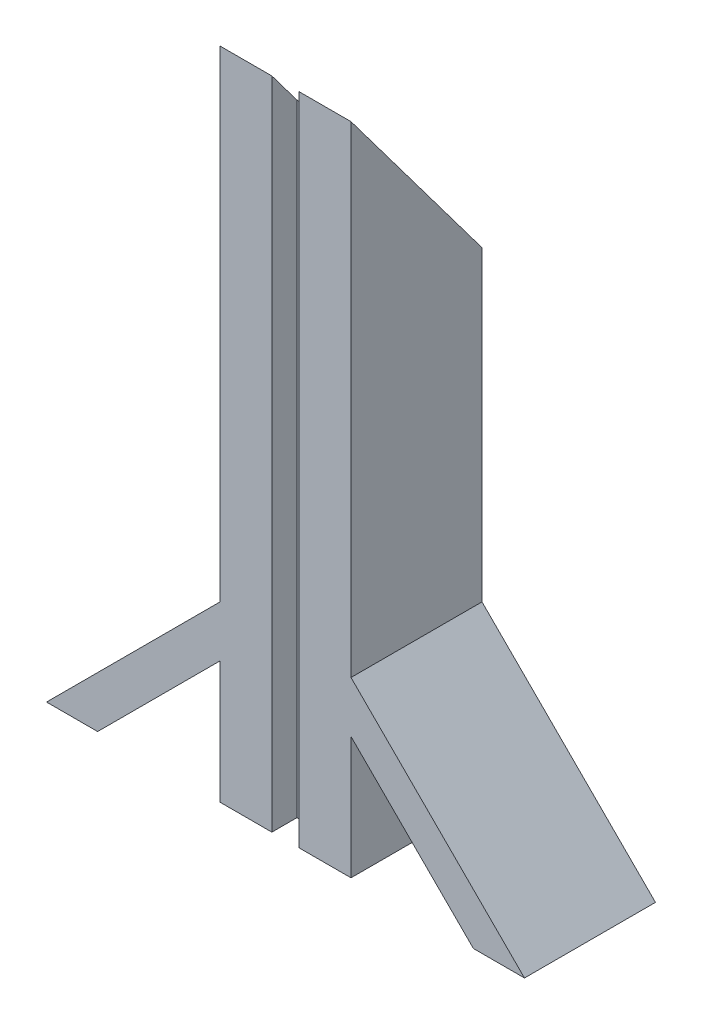
SolidWorks part; units mm, degrees
ref_plane "Front Plane" through (0, 0, 0) normal (0, 0, 1) x (1, 0, 0)
ref_plane "Top Plane" through (0, 0, 0) normal (0, 1, 0) x (1, 0, 0)
ref_plane "Right Plane" through (0, 0, 0) normal (1, 0, 0) x (0, 0, -1)
sketch "Sketch1" plane through (0, 0, 0) normal (0, 1, 0) x (1, 0, 0)
  line L1 (-15, -15) -> (15, -15)
  line L2 (-15, -15) -> (-15, 15)
  line L3 (-15, 15) -> (15, 15)
  line L4 (15, -15) -> (15, 15)
  line L5 (0, 15) -> (0, -15) construction
  line L6 (-15, 0) -> (15, 0) construction
  point P0 (0, 0)
  dimension "D1" = 30
extrude "Boss-Extrude1" add sketch "Sketch1" along normal blind 150
sketch "Sketch2" plane through (0, 0, 0) normal (0, 0, 1) x (1, 0, 0)
  line L0 (15, 39.7364) -> (54.7364, 0)
  line L1 (15, 150) -> (15, 0) construction
  line L4 (54.7364, 0) -> (43.0338, 0)
  line L5 (43.0338, 0) -> (15, 28.0338)
  line L6 (15, 39.7364) -> (15, 28.0338)
  dimension "D1" = 45
extrude "Boss-Extrude2" add sketch "Sketch2" along normal up to surface (15 mm away) and the other way up to surface (15 mm away) up to face at (0, 75, 15) other way up to face at (0, 75, -15)
mirror "Mirror1" about plane through (0, 0, 0) normal (1, 0, 0) of "Boss-Extrude2"
sketch "Sketch3" plane through (-15, 0, 0) normal (-1, 0, 0) x (0, 0, 1)
  line L0 (15, 150) -> (-15, 110)
  line L1 (-15, 150) -> (-15, 39.7364) construction
  line L2 (-15, 110) -> (-15, 150)
  line L3 (-15, 150) -> (15, 150)
  dimension "D1" = 40
extrude "Cut-Extrude1" cut sketch "Sketch3" against normal through all
sketch "Sketch4" plane through (0, 0, 0) normal (0, -1, 0) x (1, 0, 0)
  line L0 (-15, 15) -> (15, 15) construction
  line L1 (-3.125, 20.7228) -> (3.125, 20.7228)
  line L2 (-3.125, 20.7228) -> (-3.125, 9.2772)
  line L3 (-3.125, 9.2772) -> (3.125, 9.2772)
  line L4 (3.125, 20.7228) -> (3.125, 9.2772)
  line L5 (0, 9.2772) -> (0, 20.7228) construction
  line L6 (-3.125, 15) -> (3.125, 15) construction
  point P0 (0, 15)
  dimension "D1" = 6.25
extrude "Cut-Extrude2" cut sketch "Sketch4" against normal through all
